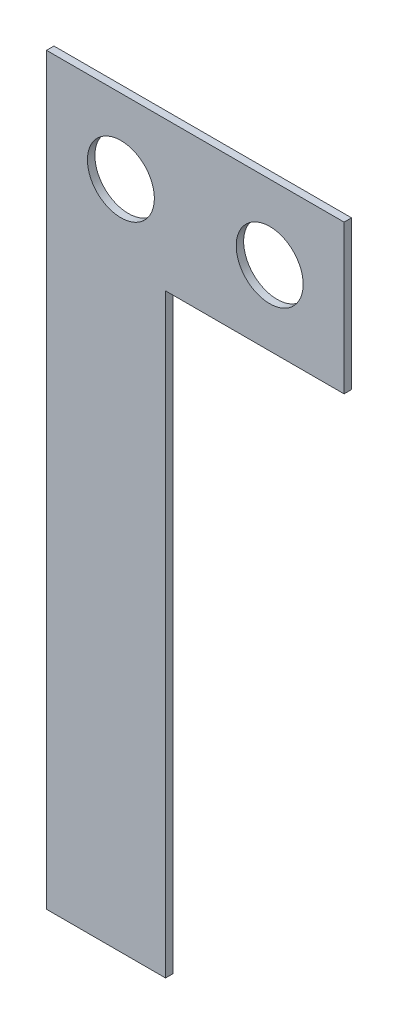
SolidWorks part; units mm, degrees
ref_plane "Plan de face" through (0, 0, 0) normal (0, 0, 1) x (1, 0, 0)
ref_plane "Plan de dessus" through (0, 0, 0) normal (0, 1, 0) x (1, 0, 0)
ref_plane "Plan de droite" through (0, 0, 0) normal (1, 0, 0) x (0, 0, -1)
sketch "Esquisse1" plane through (0, 0, 0) normal (0, 0, 1) x (1, 0, 0)
  line L0 (0, 0) -> (0, -50)
  line L1 (0, -50) -> (8, -50)
  line L2 (8, -50) -> (8, -10)
  line L3 (8, -10) -> (20, -10)
  line L4 (20, -10) -> (20, 0)
  line L5 (20, 0) -> (0, 0)
  line L6 (20, -5) -> (0, -5) construction
  circle A0 centre (15, -5) radius 1.25
  circle A1 centre (5, -5) radius 1.25
  dimension "D7" = 2.5
  dimension "D1" = 8
  dimension "D2" = 10
  dimension "D3" = 20
  dimension "D4" = 50
  dimension "D5" = 5
  dimension "D6" = 5
extrude "Boss.-Extru.1" add sketch "Esquisse1" along normal blind 0.5
hole_wizard "Dégagement M41" positions "Esquisse3" profile "Esquisse2" hole size "M4" standard "Din"
sketch "Esquisse3" plane through (0, 0, 0.5) normal (0, 0, 1) x (1, 0, 0)
  point P0 (5, -5)
  point P3 (15, -5)
sketch "Esquisse2" plane through (5, -5, 0.5) normal (1, 0, 0) x (0, -1, 0)
  line L0 (0, 0) -> (0, 16)
  line L1 (0, 16) -> (2.25, 16)
  line L2 (2.25, 16) -> (2.25, 0)
  line L5 (2.25, 0) -> (0, 0)
  line L10 (0, 16) -> (-2.25, 16) construction
  line L11 (0, -6.35) -> (0, 107.95) construction
  dimension "Diamètre du perçage" = 4.5
  dimension "Profondeur du perçage" = 16
  dimension "Angle de pointe" = 180
